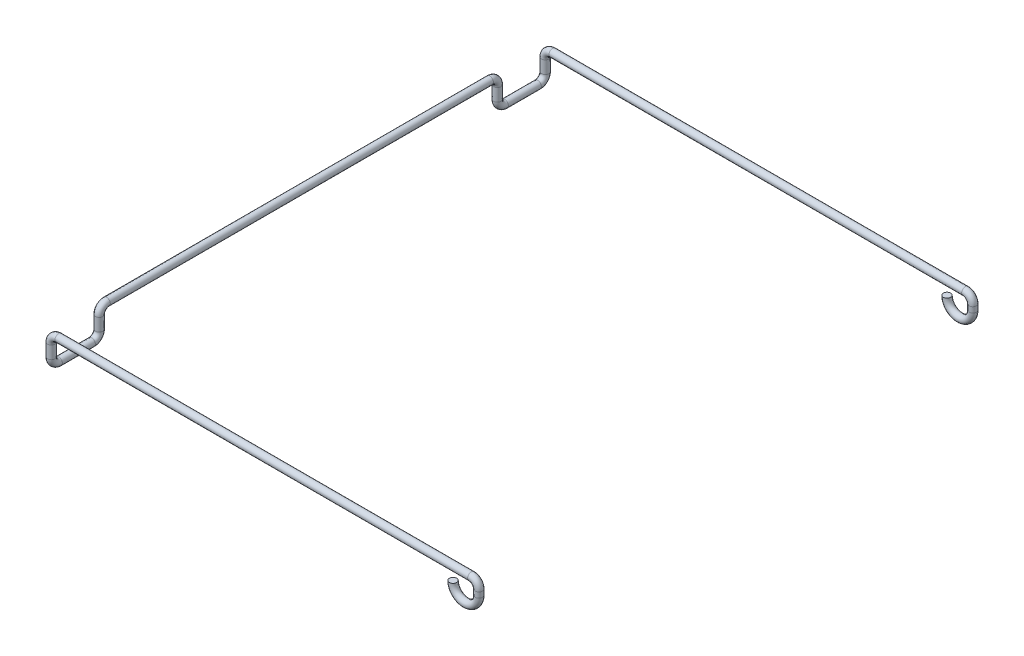
SolidWorks part; units mm, degrees
ref_plane "前视基准面" through (0, 0, 0) normal (0, 0, 1) x (1, 0, 0)
ref_plane "上视基准面" through (0, 0, 0) normal (0, 1, 0) x (1, 0, 0)
ref_plane "右视基准面" through (0, 0, 0) normal (1, 0, 0) x (0, 0, -1)
sketch3d "3D草图1"
  line L0 (-8.5785, -3.75, 28.013) -> (-8.5785, -3.75, 32.487)
  line L2 (-7.5655, 0, 33.5) -> (48.4084, 0, 33.5)
  line L4 (-7.5655, 0, -33.5) -> (48.4084, 0, -33.5)
  line L5 (-8.5785, -2.737, 27) -> (-8.5785, -1.013, 27)
  line L7 (-8.5785, -2.737, -27) -> (-8.5785, -1.013, -27)
  line L9 (-8.5785, -1.013, -33.5) -> (-8.5785, -2.737, -33.5)
  line L10 (-8.5785, 0, -25.987) -> (-8.5785, 0, 25.987)
  line L11 (-8.5785, -1.013, 33.5) -> (-8.5785, -2.737, 33.5)
  line L12 (-8.5785, -3.75, -32.487) -> (-8.5785, -3.75, -28.013)
  line L13 (49.4215, -1.013, -33.5) -> (49.4215, -1.75, -33.5)
  line L17 (49.4215, -1.013, 33.5) -> (49.4215, -1.75, 33.5)
  arc A0 (45.9215, -1.7529, -33.5) -> (49.4215, -1.75, -33.5) centre (47.6715, -1.75, -33.5) ccw
  arc A1 (45.9215, -1.75, 33.5) -> (49.4215, -1.75, 33.5) centre (47.6715, -1.75, 33.5) ccw
  arc A2 (-8.5785, -1.013, -33.5) -> (-7.5655, 0, -33.5) centre (-7.5655, -1.013, -33.5) ccw
  arc A3 (-8.5785, -3.75, -32.487) -> (-8.5785, -2.737, -33.5) centre (-8.5785, -2.737, -32.487) ccw
  arc A4 (-8.5785, -2.737, -27) -> (-8.5785, -3.75, -28.013) centre (-8.5785, -2.737, -28.013) ccw
  arc A5 (-8.5785, 0, -25.987) -> (-8.5785, -1.013, -27) centre (-8.5785, -1.013, -25.987) ccw
  arc A6 (-8.5785, -1.013, 33.5) -> (-7.5655, 0, 33.5) centre (-7.5655, -1.013, 33.5) ccw
  arc A7 (-8.5785, -2.737, 33.5) -> (-8.5785, -3.75, 32.487) centre (-8.5785, -2.737, 32.487) ccw
  arc A8 (-8.5785, -3.75, 28.013) -> (-8.5785, -2.737, 27) centre (-8.5785, -2.737, 28.013) ccw
  arc A9 (-8.5785, -1.013, 27) -> (-8.5785, 0, 25.987) centre (-8.5785, -1.013, 25.987) ccw
  arc A10 (48.4084, 0, 33.5) -> (49.4215, -1.013, 33.5) centre (48.4084, -1.013, 33.5) ccw
  arc A11 (49.4215, -1.013, -33.5) -> (48.4084, 0, -33.5) centre (48.4084, -1.013, -33.5) ccw
  point P6 (-8.5785, -1.875, -27)
  point P11 (-8.5785, -1.875, 33.5)
  point P15 (47.6715, -1.75, -31.75)
  point P22 (47.6715, -1.75, 35.25)
  point P23 (-8.5785, 0, -33.5)
  point P25 (-7.5655, -1.013, -34.513)
  point P28 (-8.5785, -3.75, -33.5)
  point P29 (-7.5655, -2.737, -32.487)
  point P32 (-8.5785, -3.75, -27)
  point P33 (-7.5655, -2.737, -28.013)
  point P36 (-8.5785, 0, -27)
  point P37 (-9.5916, -1.013, -25.987)
  point P40 (-8.5785, 0, 33.5)
  point P41 (-7.5655, -1.013, 32.487)
  point P44 (-8.5785, -3.75, 33.5)
  point P45 (-7.5655, -2.737, 32.487)
  point P48 (-8.5785, -3.75, 27)
  point P49 (-7.5655, -2.737, 28.013)
  point P52 (-8.5785, 0, 27)
  point P54 (-9.5916, -1.013, 25.987)
  point P57 (49.4215, 0, 33.5)
  point P59 (48.4084, -1.013, 32.487)
  point P62 (49.4215, 0, -33.5)
  point P63 (48.4084, -1.013, -32.487)
  dimension "D13" = 3.5
  dimension "D14" = 1.013
  dimension "D1" = 67
  dimension "D2" = 3.75
  dimension "D3" = 6.5
  dimension "D4" = 6.5
  dimension "D5" = 58
  dimension "D12" = 58
  dimension "D6" = 90
  dimension "D7" = 90
  dimension "D8" = 90
  dimension "D9" = 90
  dimension "D10" = 33.5
  dimension "D11" = 0
sketch "草图1" plane through (0, 0, 0) normal (0, 0, 1) x (1, 0, 0)
  circle A0 centre (-8.5785, 0) radius 0.5
  dimension "D1" = 1
sweep "扫描1" add profiles "草图1" path "3D草图1"
